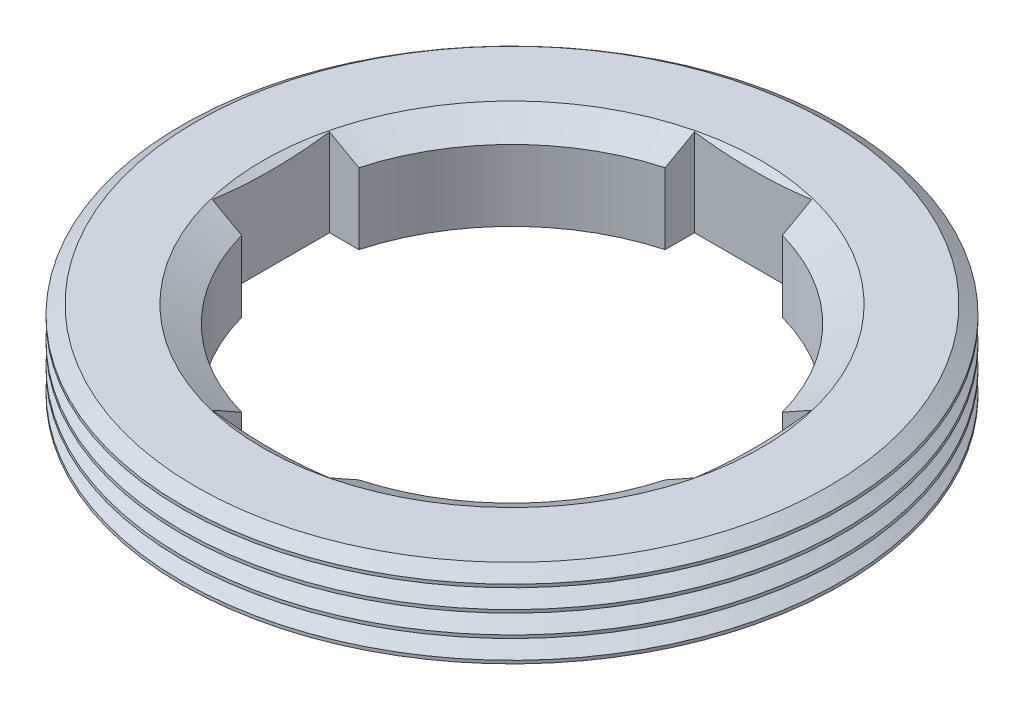
SolidWorks part; units mm, degrees
material " 09Г2С ГОСТ 4543-71"
ref_plane "Спереди" through (0, 0, 0) normal (0, 0, 1) x (1, 0, 0)
ref_plane "Сверху" through (0, 0, 0) normal (0, 1, 0) x (1, 0, 0)
ref_plane "Слева" through (0, 0, 0) normal (1, 0, 0) x (0, 0, -1)
sketch "Эскиз1" plane through (0, 0, 0) normal (0, 1, 0) x (1, 0, 0)
  circle A0 centre (0, 0) radius 15
  circle A1 centre (0, 0) radius 22.5
  dimension "D1" = 30
  dimension "D2" = 45
  dimension "D3" = 7.5
extrude "Вытянуть1" add sketch "Эскиз1" along normal blind 6
sketch "Эскиз2" plane through (0, 0, 0) normal (1, 0, 0) x (0, 0, -1)
  line L0 (0, 0) -> (0, 11.8167) construction
  line L1 (-17, 6) -> (-15, 6) construction
  line L2 (-15, 6) -> (-15, 4.8453) construction
  line L3 (-15, 4.8453) -> (-17, 6) construction
  line L4 (22.5, 6) -> (-22.5, 6) construction
  line L5 (15, 6) -> (-15, 6) construction
  line L6 (-22.5, 6) -> (-17.2196, 6) construction
  line L7 (-21.58, 6) -> (-22.5, 5.3558)
  line L8 (-22.5, 5.3558) -> (-25, 5.3558)
  line L9 (-25, 5.3558) -> (-25, 6.6442)
  line L10 (-22.5, 6) -> (-22.5, 0) construction
  line L11 (-22.5, 6.6442) -> (-25, 6.6442)
  line L12 (-21.58, 6) -> (-22.5, 6.6442)
  point P21 (-25, 6)
  dimension "D1" = 30
  dimension "D2" = 34
  dimension "D3" = 70
  dimension "D4" = 43.16
  dimension "D5" = 50
  dimension "D6" = 0.6442
revolve "М45х1,5 1й зуб" cut sketch "Эскиз2" angle 360 about L0
sketch "Эскиз3" plane through (0, 0, 0) normal (1, 0, 0) x (0, 0, -1)
  line L0 (0, 0) -> (0, 11.8167) construction
  line L1 (-15, 4.8453) -> (-17, 6) construction
  line L2 (-17, 6) -> (-15, 6) construction
  line L3 (-15, 6) -> (-15, 4.8453) construction
  line L4 (0, 0) -> (0, 11.8167) construction
  line L5 (-15, 4.8453) -> (-17, 6)
  line L6 (-17, 6) -> (-15, 6)
  line L7 (-15, 6) -> (-15, 4.8453)
revolve "Вырез-Повернуть2" cut sketch "Эскиз3" angle 360 about L4
pattern_linear "М45х1,5 массив1" count 5 spacing 1.5 along (0, -1, 0) of "М45х1,5 1й зуб"
sketch "Эскиз4" plane through (0, 6, 0) normal (0, 1, 0) x (1, 0, 0)
  line L0 (0, 0) -> (16.4568, 0) construction
  line L2 (14.4568, 4) -> (16.4568, 4)
  line L3 (14.4568, 4) -> (14.4568, -4)
  line L4 (14.4568, -4) -> (16.4568, -4)
  line L5 (16.4568, 4) -> (16.4568, -4)
  circle A0 centre (0, 0) radius 15 construction
  dimension "D1" = 8
  dimension "D2" = 2
extrude "Вытянуть2" cut sketch "Эскиз4" against normal through all
pattern_circular "Круговой массив1" count 4 over 360 about axis through (0, 0, 0) along (0, 1, 0) of "Вытянуть2"
